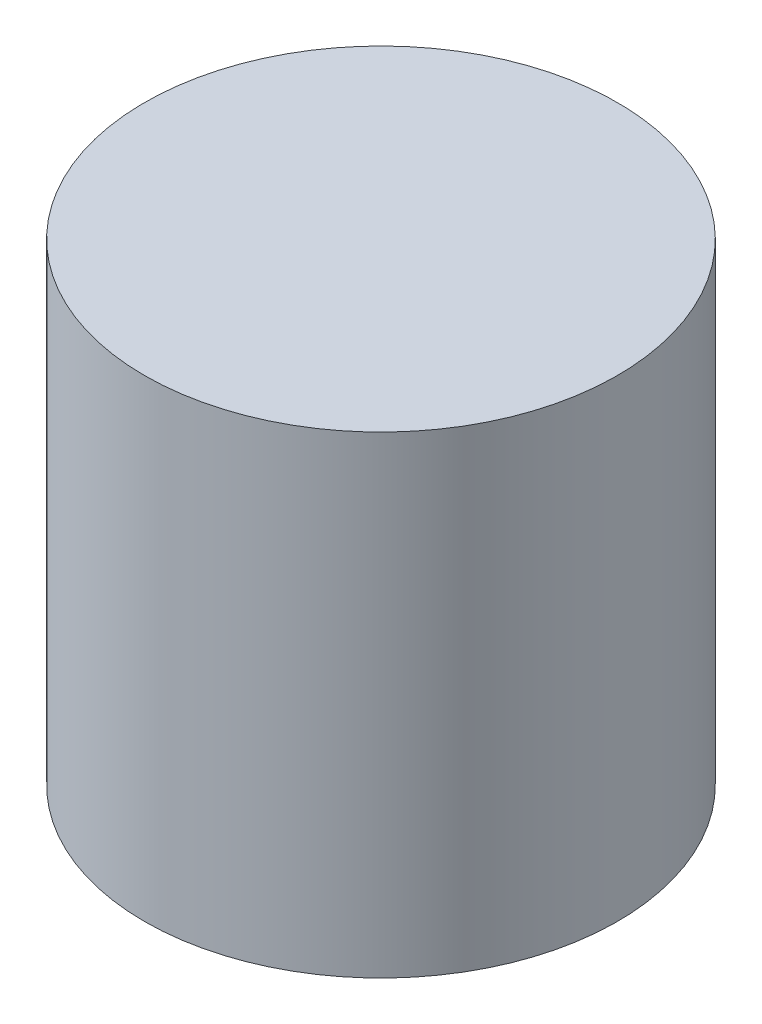
SolidWorks part; units mm, degrees
ref_plane "Front Plane" through (0, 0, 0) normal (0, 0, 1) x (1, 0, 0)
ref_plane "Top Plane" through (0, 0, 0) normal (0, 1, 0) x (1, 0, 0)
ref_plane "Right Plane" through (0, 0, 0) normal (1, 0, 0) x (0, 0, -1)
sketch "Sketch1" plane through (0, 0, 0) normal (0, 1, 0) x (1, 0, 0)
  circle A0 centre (0, 0) radius 7.5
  dimension "D1" = 15
extrude "Boss-Extrude1" add sketch "Sketch1" along normal blind 15
